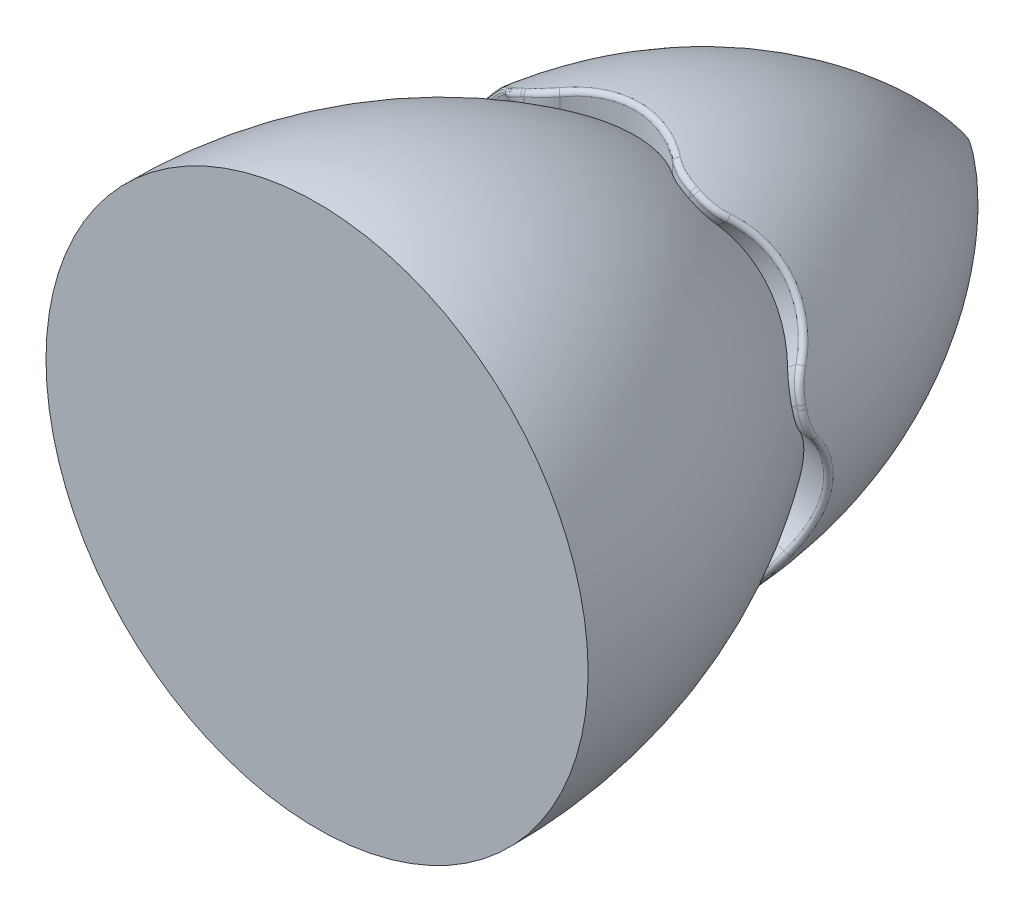
SolidWorks part; units mm, degrees
ref_plane "Přední rovina" through (0, 0, 0) normal (0, 0, 1) x (1, 0, 0)
ref_plane "Horní rovina" through (0, 0, 0) normal (0, 1, 0) x (1, 0, 0)
ref_plane "Pravá rovina" through (0, 0, 0) normal (1, 0, 0) x (0, 0, -1)
sketch "Skica1" plane through (0, 0, 0) normal (0, 1, 0) x (1, 0, 0)
  line L0 (0, 0) -> (0, 81.5164) construction
  line L1 (0, 0) -> (45, 0)
  line L2 (0, 0) -> (0, 81.5164)
  arc A0 (0, 81.5164) -> (45, 0) centre (-62.477, -6.1521) cw
  dimension "D1" = 45
revolve "Rotovat1" add sketch "Skica1" angle 360 about L0
sketch "Skica2" plane through (0, 0, 0) normal (0, 1, 0) x (1, 0, 0)
  line L0 (-45, 0) -> (45, 0) construction
  line L1 (15, 0) -> (-15, 0)
  arc A0 (-15, 0) -> (15, 0) centre (0, -15) cw
  dimension "D1" = 30
  dimension "D2" = 15
extrude "Odebrat vysunutím1" cut sketch "Skica2" along normal through all
pattern_circular "Kruhové pole1" count 7 over 360 about axis through (0, 0, 0) along (0, 0, -1) of "Odebrat vysunutím1"
fillet "Zaoblit1" radius 10 14 edges at (-38.1137, 11.2089, 0) (-19.409, 34.6639, 0) (-15, 36.7871, 0) (15, 36.7871, 0) (19.409, 34.6639, 0) (38.1137, 11.2089, 0) (39.2026, 6.438, 0) (32.527, -22.8098, 0) (29.4759, -26.6358, 0) (2.4468, -39.6523, 0) (-2.4468, -39.6523, 0) (-29.4759, -26.6358, 0) (-32.527, -22.8098, 0) (-39.2026, 6.438, 0)
fillet "Zaoblit2" radius 1 28 edges at (19.5248, 40.5436, 0) (15.6155, 42.1731, -0.4839) (-2.4493, 44.4122, -6.0713) (-15.4359, 42.2351, -0.5438) (-19.5248, 40.5436, 0) (-23.2361, 38.5031, -0.4839) (-36.25, 25.7756, -6.0713) (-42.6449, 14.2649, -0.5438) (-43.8718, 10.0134, 0) (-44.5905, 5.8396, -0.4839) (-42.7537, -12.2706, -6.0713) (-37.7414, -24.4471, -0.5438) (-35.1824, -28.057, 0) (-32.3673, -31.2213, -0.4839) (-17.063, -41.0768, -6.0713) (-4.4178, -44.75, -0.5438) (0, -45, 0) (4.2292, -44.7719, -0.4839) (21.4765, -38.9513, -6.0713) (32.2324, -31.3551, -0.5438) (35.1824, -28.057, 0) (37.6409, -24.6083, -0.4839) (43.8438, -7.4947, -6.0713) (44.611, 5.6507, -0.5438) (43.8718, 10.0134, 0) (42.7083, 14.0858, -0.4839) (33.1958, 29.6055, -6.0713) (23.3966, 38.4015, -0.5438)
sketch "Skica3" plane through (0, 0, 0) normal (0, 1, 0) x (1, 0, 0)
  line L0 (0, 41.1669) -> (0, -65.4884)
  line L1 (0, -65.4884) -> (-61.1469, -65.4884)
  arc A0 (-61.1469, -65.4884) -> (0, 41.1669) centre (61.1205, -64.7301) cw
  point P5 (0, 29.1252)
  point P6 (0, 41.1669)
  point P7 (-61.1469, -65.4884)
revolve "Rotovat2" add sketch "Skica3" angle 360 about L0
